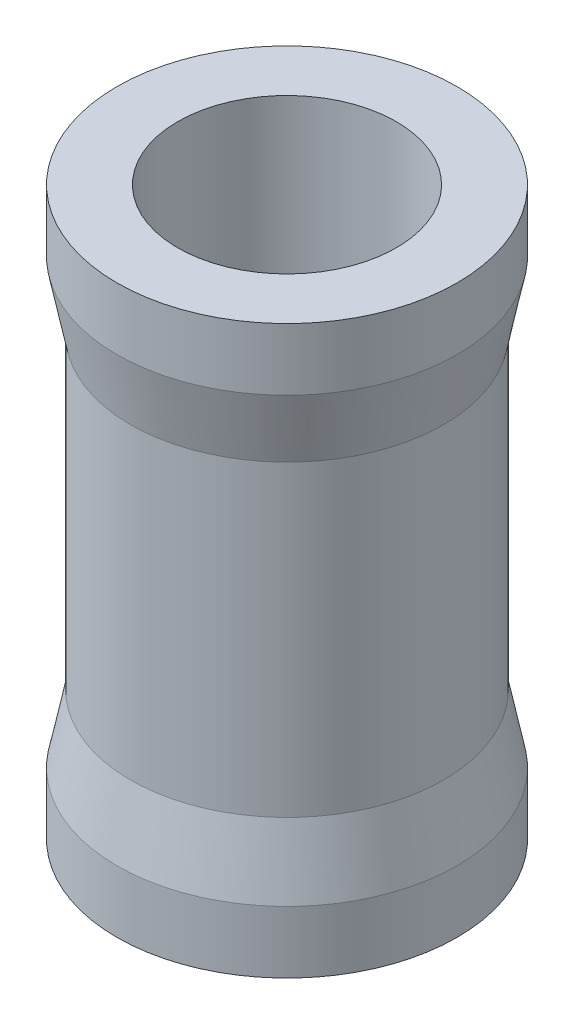
SolidWorks part; units mm, degrees
ref_plane "Front Plane" through (0, 0, 0) normal (0, 0, 1) x (1, 0, 0)
ref_plane "Top Plane" through (0, 0, 0) normal (0, 1, 0) x (1, 0, 0)
ref_plane "Right Plane" through (0, 0, 0) normal (1, 0, 0) x (0, 0, -1)
sketch "Sketch1" plane through (0, 0, 0) normal (0, 0, 1) x (1, 0, 0)
  line L0 (0, 10.5) -> (0, -8.9952) construction
  line L1 (10.3595, 0) -> (0, 0) construction
  line L2 (4.05, 10.5) -> (6.3, 10.5)
  line L3 (6.3, 10.5) -> (6.3, 8.2)
  line L4 (6.3, 8.2) -> (5.8, 5.7)
  line L5 (5.8, 5.7) -> (5.8, -5.7)
  line L6 (4.05, 10.5) -> (4.05, -10.5)
  line L7 (6.3, -8.2) -> (5.8, -5.7)
  line L8 (6.3, -10.5) -> (6.3, -8.2)
  line L9 (4.05, -10.5) -> (6.3, -10.5)
  point P12 (4.05, 0)
  point P13 (5.8, 0)
  dimension "D1" = 6.3
  dimension "D2" = 5.8
  dimension "D3" = 2.5
  dimension "D4" = 11.4
  dimension "D5" = 2.3
  dimension "D6" = 4.05
revolve "Revolve1" add sketch "Sketch1" angle 360 about L0
